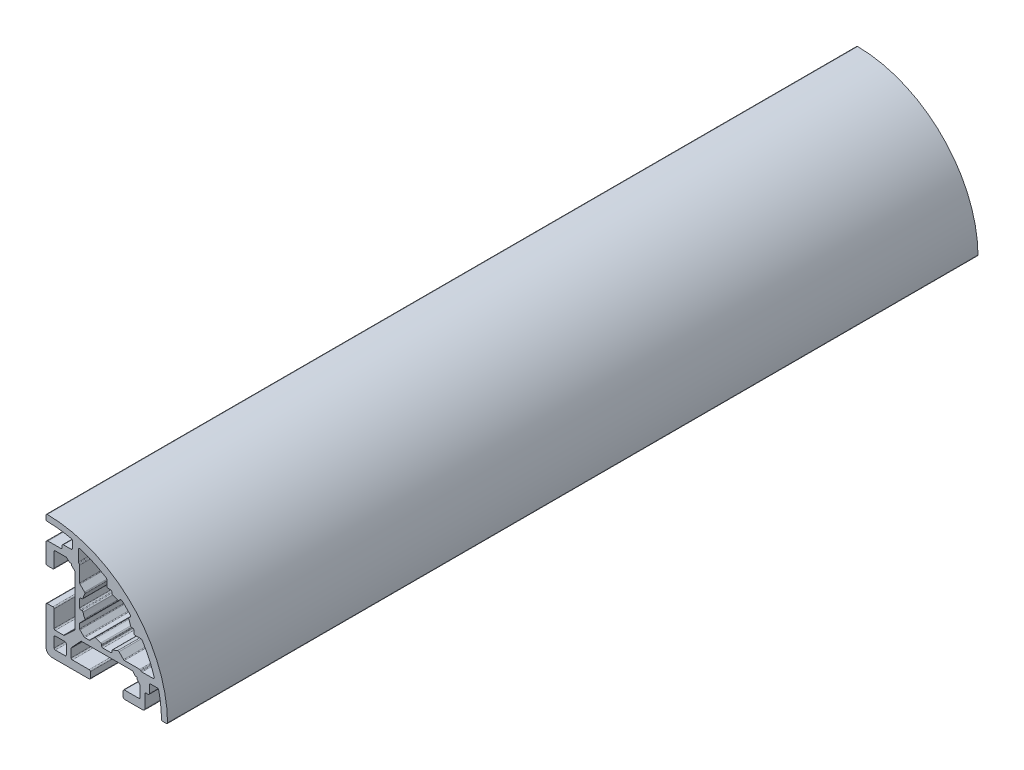
SolidWorks part; units mm, degrees
ref_plane "Plano frontal" through (0, 0, 0) normal (0, 0, 1) x (1, 0, 0)
ref_plane "Plano superior" through (0, 0, 0) normal (0, 1, 0) x (1, 0, 0)
ref_plane "Plano direito" through (0, 0, 0) normal (1, 0, 0) x (0, 0, -1)
ref_plane "Plano1" through (0, 0, 0) normal (0, 0, -1) x (-1, 0, 0)
sketch "Esboço1" plane through (0, 0, 0) normal (0, 0, -1) x (-1, 0, 0)
  line L0 (12.7, -13) -> (10.3, -13)
  line L1 (10, -12.7) -> (10, -10.3)
  line L2 (10.3, -10) -> (12.7, -10)
  line L3 (13, -10.3) -> (13, -12.7)
  line L4 (-0.95, 6.7) -> (-0.3, 6.7)
  line L5 (0, 7) -> (0, 8.4776)
  line L6 (7, 11.4273) -> (7, 8.6799)
  line L7 (6.9121, 8.4678) -> (6.7879, 8.3435)
  line L8 (6.7, 8.1314) -> (6.7, 4.3494)
  line L9 (6.6121, 4.1372) -> (5.4871, 3.0123)
  line L10 (6.1579, 1.25) -> (6.4, 1.25)
  line L11 (6.7, 0.95) -> (6.7, -0.95)
  line L12 (6.4, -1.25) -> (6.1579, -1.25)
  line L13 (5.4871, -3.0123) -> (6.6121, -4.1372)
  line L14 (6.7, -4.3494) -> (6.7, -5.4396)
  line L15 (6.6121, -5.6517) -> (5.6517, -6.6121)
  line L16 (5.4395, -6.7) -> (4.3494, -6.7)
  line L17 (4.1373, -6.6121) -> (3.0123, -5.4871)
  line L18 (1.25, -6.1579) -> (1.25, -6.4)
  line L19 (0.95, -6.7) -> (-0.95, -6.7)
  line L20 (-1.25, -6.4) -> (-1.25, -6.1579)
  line L21 (-3.0123, -5.4871) -> (-4.1373, -6.6121)
  line L22 (-4.3494, -6.7) -> (-8.1314, -6.7)
  line L23 (-8.3435, -6.7879) -> (-8.4678, -6.9121)
  line L24 (-8.6799, -7) -> (-11.4273, -7)
  line L25 (-8.4777, 0) -> (-7, 0)
  line L26 (-6.7, 0.3) -> (-6.7, 0.95)
  line L27 (-6.4, 1.25) -> (-6.1579, 1.25)
  line L28 (-5.4871, 3.0123) -> (-5.7974, 3.3226)
  line L29 (-3.3226, 5.7974) -> (-3.0123, 5.4871)
  line L30 (-1.25, 6.1579) -> (-1.25, 6.4)
  line L31 (7.9882, 6.4323) -> (8.7045, 7.0724)
  line L32 (8.7045, 7.0724) -> (8.7283, 7.4961)
  line L33 (8.7283, 7.4961) -> (9.1516, 7.4723)
  line L34 (9.1516, 7.4723) -> (9.8678, 8.1124)
  line L35 (10.08, 8.2002) -> (12.7001, 8.2002)
  line L36 (13.0001, 7.9002) -> (13, 4.3502)
  line L37 (13.3, 4.0502) -> (14.7, 4.0502)
  line L38 (15, 4.3502) -> (15, 8.8999)
  line L39 (14.5, 9.3999) -> (11.3, 9.3999)
  line L40 (11, 9.6999) -> (11, 10.1999)
  line L41 (10.7, 10.4999) -> (8.8, 10.4999)
  line L42 (8.5, 10.7999) -> (8.5, 12.51)
  line L43 (15, 13.7984) -> (15, 14.6985)
  line L44 (-14.6985, -15) -> (-13.7984, -15)
  line L45 (-12.5105, -8.5) -> (-10.8005, -8.5)
  line L46 (-10.5005, -8.8) -> (-10.5005, -10.7)
  line L47 (-10.2005, -11) -> (-9.7004, -11)
  line L48 (-9.4004, -11.3) -> (-9.4004, -14.5)
  line L49 (-8.9004, -15) -> (-4.3505, -15)
  line L50 (-4.0505, -14.7) -> (-4.0504, -13.3)
  line L51 (-4.3504, -13) -> (-7.9005, -12.9999)
  line L52 (-8.2005, -12.6999) -> (-8.2004, -10.0799)
  line L53 (-8.1126, -9.8677) -> (-7.4725, -9.1515)
  line L54 (-7.4725, -9.1515) -> (-7.4963, -8.728)
  line L55 (-7.4963, -8.728) -> (-7.0727, -8.7042)
  line L56 (-7.0727, -8.7042) -> (-6.4326, -7.988)
  line L57 (-6.2205, -7.9001) -> (6.2197, -7.9001)
  line L58 (6.4318, -7.988) -> (8.7117, -10.4679)
  line L59 (8.7996, -10.6801) -> (8.7996, -12.7001)
  line L60 (8.4996, -13.0001) -> (4.3496, -13.0001)
  line L61 (4.0496, -13.3001) -> (4.0496, -14.7)
  line L62 (4.3496, -15) -> (13.5, -15)
  line L63 (15, -13.5) -> (15, -4.35)
  line L64 (14.7, -4.05) -> (13.2999, -4.05)
  line L65 (12.9999, -4.35) -> (12.9999, -8.4999)
  line L66 (12.6999, -8.7999) -> (10.6798, -8.7999)
  line L67 (10.4677, -8.712) -> (7.9878, -6.4321)
  line L68 (7.9003, -6.22) -> (7.9003, 6.2202)
  arc A0 (10.3, -13) -> (10, -12.7) centre (10.3, -12.7) cw
  arc A1 (10, -10.3) -> (10.3, -10) centre (10.3, -10.3) cw
  arc A2 (12.7, -10) -> (13, -10.3) centre (12.7, -10.3) cw
  arc A3 (13, -12.7) -> (12.7, -13) centre (12.7, -12.7) cw
  arc A4 (-0.3, 6.7) -> (0, 7) centre (-0.3, 7) ccw
  arc A5 (0, 8.4776) -> (0.1408, 8.7319) centre (0.3, 8.4776) cw
  arc A6 (0.1408, 8.7319) -> (6.6101, 11.7135) centre (15, -15) cw
  arc A7 (6.6101, 11.7135) -> (7, 11.4273) centre (6.7, 11.4273) cw
  arc A8 (7, 8.6799) -> (6.9121, 8.4678) centre (6.7, 8.6799) cw
  arc A9 (6.7879, 8.3435) -> (6.7, 8.1314) centre (7, 8.1314) ccw
  arc A10 (6.7, 4.3494) -> (6.6121, 4.1372) centre (6.4, 4.3494) cw
  arc A11 (5.4871, 3.0123) -> (5.43, 2.6678) centre (5.6993, 2.8001) ccw
  arc A12 (5.43, 2.6678) -> (5.867, 1.4768) centre (0, 0) cw
  arc A13 (5.867, 1.4768) -> (6.1579, 1.25) centre (6.1579, 1.55) ccw
  arc A14 (6.4, 1.25) -> (6.7, 0.95) centre (6.4, 0.95) cw
  arc A15 (6.7, -0.95) -> (6.4, -1.25) centre (6.4, -0.95) cw
  arc A16 (6.1579, -1.25) -> (5.867, -1.4768) centre (6.1579, -1.55) ccw
  arc A17 (5.867, -1.4768) -> (5.43, -2.6678) centre (0, 0) cw
  arc A18 (5.43, -2.6678) -> (5.4871, -3.0123) centre (5.6993, -2.8001) ccw
  arc A19 (6.6121, -4.1372) -> (6.7, -4.3494) centre (6.4, -4.3494) cw
  arc A20 (6.7, -5.4396) -> (6.6121, -5.6517) centre (6.4, -5.4396) cw
  arc A21 (5.6517, -6.6121) -> (5.4395, -6.7) centre (5.4395, -6.4) cw
  arc A22 (4.3494, -6.7) -> (4.1373, -6.6121) centre (4.3494, -6.4) cw
  arc A23 (3.0123, -5.4871) -> (2.6678, -5.43) centre (2.8001, -5.6993) ccw
  arc A24 (2.6678, -5.43) -> (1.4768, -5.867) centre (0, 0) cw
  arc A25 (1.4768, -5.867) -> (1.25, -6.1579) centre (1.55, -6.1579) ccw
  arc A26 (1.25, -6.4) -> (0.95, -6.7) centre (0.95, -6.4) cw
  arc A27 (-0.95, -6.7) -> (-1.25, -6.4) centre (-0.95, -6.4) cw
  arc A28 (-1.25, -6.1579) -> (-1.4768, -5.867) centre (-1.55, -6.1579) ccw
  arc A29 (-1.4768, -5.867) -> (-2.6678, -5.43) centre (0, 0) cw
  arc A30 (-2.6678, -5.43) -> (-3.0123, -5.4871) centre (-2.8001, -5.6993) ccw
  arc A31 (-4.1373, -6.6121) -> (-4.3494, -6.7) centre (-4.3494, -6.4) cw
  arc A32 (-8.1314, -6.7) -> (-8.3435, -6.7879) centre (-8.1314, -7) ccw
  arc A33 (-8.4678, -6.9121) -> (-8.6799, -7) centre (-8.6799, -6.7) cw
  arc A34 (-11.4273, -7) -> (-11.7135, -6.6101) centre (-11.4273, -6.7) cw
  arc A35 (-11.7135, -6.6101) -> (-8.7319, -0.1408) centre (15, -15) cw
  arc A36 (-8.7319, -0.1408) -> (-8.4777, 0) centre (-8.4777, -0.3) cw
  arc A37 (-7, 0) -> (-6.7, 0.3) centre (-7, 0.3) ccw
  arc A38 (-6.7, 0.95) -> (-6.4, 1.25) centre (-6.4, 0.95) cw
  arc A39 (-6.1579, 1.25) -> (-5.867, 1.4768) centre (-6.1579, 1.55) ccw
  arc A40 (-5.867, 1.4768) -> (-5.43, 2.6678) centre (0, 0) cw
  arc A41 (-5.43, 2.6678) -> (-5.4871, 3.0123) centre (-5.6993, 2.8001) ccw
  arc A42 (-5.7974, 3.3226) -> (-5.8083, 3.7354) centre (-5.5853, 3.5347) cw
  arc A43 (-5.8083, 3.7354) -> (-3.7354, 5.8083) centre (15, -15) cw
  arc A44 (-3.7354, 5.8083) -> (-3.3226, 5.7974) centre (-3.5347, 5.5853) cw
  arc A45 (-3.0123, 5.4871) -> (-2.6678, 5.43) centre (-2.8001, 5.6993) ccw
  arc A46 (-2.6678, 5.43) -> (-1.4768, 5.867) centre (0, 0) cw
  arc A47 (-1.4768, 5.867) -> (-1.25, 6.1579) centre (-1.55, 6.1579) ccw
  arc A48 (-1.25, 6.4) -> (-0.95, 6.7) centre (-0.95, 6.4) cw
  arc A49 (9.8678, 8.1124) -> (10.08, 8.2002) centre (10.08, 7.9002) cw
  arc A50 (12.7001, 8.2002) -> (13.0001, 7.9002) centre (12.7001, 7.9002) cw
  arc A51 (13, 4.3502) -> (13.3, 4.0502) centre (13.3, 4.3502) ccw
  arc A52 (14.7, 4.0502) -> (15, 4.3502) centre (14.7, 4.3502) ccw
  arc A53 (15, 8.8999) -> (14.5, 9.3999) centre (14.5, 8.8999) ccw
  arc A54 (11.3, 9.3999) -> (11, 9.6999) centre (11.3, 9.6999) cw
  arc A55 (11, 10.1999) -> (10.7, 10.4999) centre (10.7, 10.1999) ccw
  arc A56 (8.8, 10.4999) -> (8.5, 10.7999) centre (8.8, 10.7999) cw
  arc A57 (8.5, 12.51) -> (8.734, 12.8026) centre (8.8, 12.51) cw
  arc A58 (8.734, 12.8026) -> (14.7031, 13.4984) centre (15, -15) cw
  arc A59 (14.7031, 13.4984) -> (15, 13.7984) centre (14.7, 13.7984) ccw
  arc A60 (15, 14.6985) -> (14.697, 14.9985) centre (14.7, 14.6985) ccw
  arc A61 (14.697, 14.9985) -> (-14.9985, -14.697) centre (15, -15) ccw
  arc A62 (-14.9985, -14.697) -> (-14.6985, -15) centre (-14.6985, -14.7) ccw
  arc A63 (-13.7984, -15) -> (-13.4985, -14.7031) centre (-13.7984, -14.7) ccw
  arc A64 (-13.4985, -14.7031) -> (-12.8027, -8.734) centre (15, -15) cw
  arc A65 (-12.8027, -8.734) -> (-12.5105, -8.5) centre (-12.51, -8.8) cw
  arc A66 (-10.8005, -8.5) -> (-10.5005, -8.8) centre (-10.8005, -8.8) cw
  arc A67 (-10.5005, -10.7) -> (-10.2005, -11) centre (-10.2005, -10.7) ccw
  arc A68 (-9.7004, -11) -> (-9.4004, -11.3) centre (-9.7004, -11.3) cw
  arc A69 (-9.4004, -14.5) -> (-8.9004, -15) centre (-8.9004, -14.5) ccw
  arc A70 (-4.3505, -15) -> (-4.0505, -14.7) centre (-4.3505, -14.7) ccw
  arc A71 (-4.0504, -13.3) -> (-4.3504, -13) centre (-4.3504, -13.3) ccw
  arc A72 (-7.9005, -12.9999) -> (-8.2005, -12.6999) centre (-7.9005, -12.6999) cw
  arc A73 (-8.2004, -10.0799) -> (-8.1126, -9.8677) centre (-7.9004, -10.0799) cw
  arc A74 (-6.4326, -7.988) -> (-6.2205, -7.9001) centre (-6.2205, -8.2001) cw
  arc A75 (6.2197, -7.9001) -> (6.4318, -7.988) centre (6.2197, -8.2001) cw
  arc A76 (8.7117, -10.4679) -> (8.7996, -10.6801) centre (8.4996, -10.6801) cw
  arc A77 (8.7996, -12.7001) -> (8.4996, -13.0001) centre (8.4996, -12.7001) cw
  arc A78 (4.3496, -13.0001) -> (4.0496, -13.3001) centre (4.3496, -13.3001) ccw
  arc A79 (4.0496, -14.7) -> (4.3496, -15) centre (4.3496, -14.7) ccw
  arc A80 (13.5, -15) -> (15, -13.5) centre (13.5, -13.5) ccw
  arc A81 (15, -4.35) -> (14.7, -4.05) centre (14.7, -4.35) ccw
  arc A82 (13.2999, -4.05) -> (12.9999, -4.35) centre (13.2999, -4.35) ccw
  arc A83 (12.9999, -8.4999) -> (12.6999, -8.7999) centre (12.6999, -8.4999) cw
  arc A84 (10.6798, -8.7999) -> (10.4677, -8.712) centre (10.6798, -8.4999) cw
  arc A85 (7.9878, -6.4321) -> (7.9003, -6.22) centre (8.2003, -6.2204) cw
  arc A86 (7.9003, 6.2202) -> (7.9882, 6.4323) centre (8.2003, 6.2202) cw
  dimension "D1" = 30
  dimension "D2" = 1.5
extrude "Ressalto-extrusão1" add sketch "Esboço1" against normal blind 200
